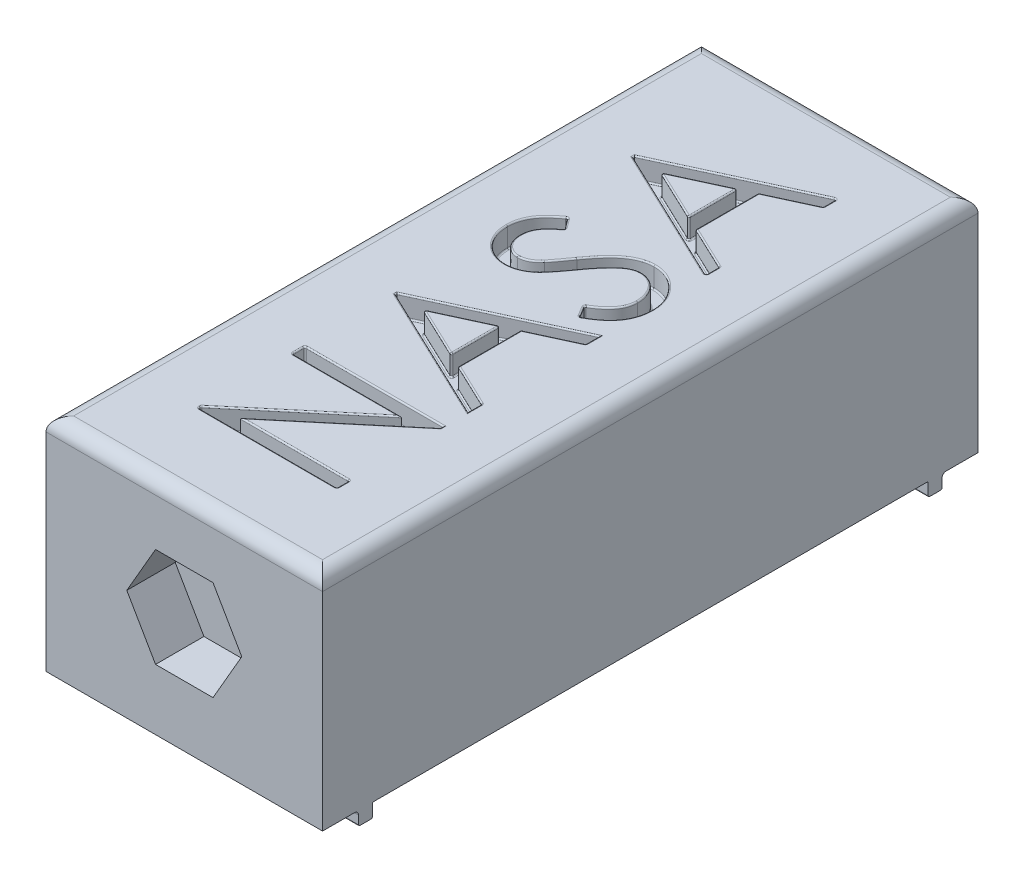
SolidWorks part; units mm, degrees
ref_plane "Front Plane" through (0, 0, 0) normal (0, 0, 1) x (1, 0, 0)
ref_plane "Top Plane" through (0, 0, 0) normal (0, 1, 0) x (1, 0, 0)
ref_plane "Right Plane" through (0, 0, 0) normal (1, 0, 0) x (0, 0, -1)
sketch "Sketch1" plane through (0, 0, 0) normal (0, 1, 0) x (1, 0, 0)
  line L1 (-10, 20) -> (10, 20)
  line L2 (-10, 20) -> (-10, -20)
  line L3 (-10, -20) -> (10, -20)
  line L4 (10, 20) -> (10, -20)
  line L5 (-10, 20) -> (10, -20) construction
  line L6 (-10, -20) -> (10, 20) construction
  point P4 (0, 0)
  dimension "D1" = 40
  dimension "D2" = 20
extrude "Boss-Extrude1" add sketch "Sketch1" along normal blind 16
sketch "Sketch2" plane through (0, 0, 0) normal (0, -1, 0) x (1, 0, 0)
  line L0 (-10, 0) -> (10, 0) construction
  line L1 (-10, 23.7) -> (10, 23.7)
  line L2 (-10, 23.7) -> (-10, 20)
  line L3 (-10, 20) -> (10, 20)
  line L4 (10, 23.7) -> (10, 20)
  line L5 (-10, 23.7) -> (10, 20) construction
  line L6 (-10, 20) -> (10, 23.7) construction
  line L11 (-10, -20) -> (10, -23.7) construction
  line L12 (-10, -23.7) -> (10, -20) construction
  line L13 (-10, -20) -> (-10, 20) construction
  line L14 (10, 20) -> (10, -20) construction
  line L15 (10, -23.7) -> (10, -20)
  line L16 (-10, -20) -> (10, -20)
  line L17 (-10, -23.7) -> (-10, -20)
  line L18 (-10, -23.7) -> (10, -23.7)
  point P4 (0, 21.85)
  point P12 (0, -21.85)
  dimension "D1" = 3.7
extrude "Boss-Extrude2" add sketch "Sketch2" against normal blind 16 contours L2 L1 L4 L3 | L15 L16 L17 L18
sketch "Sketch3" plane through (0, 0, -23.7) normal (0, 0, -1) x (-1, 0, 0)
  line L0 (-10, 16) -> (10, 0) construction
  line L1 (10, 16) -> (-10, 0) construction
  line L2 (10, 0) -> (-10, 0) construction
  line L3 (2.0785, 11.6) -> (-2.0785, 11.6)
  line L4 (-2.0785, 11.6) -> (-4.1569, 8)
  line L5 (-4.1569, 8) -> (-2.0785, 4.4)
  line L6 (-2.0785, 4.4) -> (2.0785, 4.4)
  line L7 (2.0785, 4.4) -> (4.1569, 8)
  line L8 (4.1569, 8) -> (2.0785, 11.6)
  line L9 (10, 16) -> (10, 0) construction
  circle A1 centre (0, 8) radius 3.6 construction
  point P1 (0, 0)
  point P4 (10, 16)
  point P5 (10, 0)
  point P8 (0, 0)
  point P11 (-10, 0)
  point P21 (-10, 16)
  point P23 (0, 0)
  point P24 (10, 0)
  point P25 (-10, 16)
  point P26 (10, 0)
  dimension "D1" = 7.2
extrude "Cut-Extrude8" cut sketch "Sketch3" against normal blind 3.5
fillet "Fillet1" radius 1 4 edges at (0, 16, 23.7) (10, 16, 0) (-10, 16, 0) (0, 16, -23.7)
sketch "Sketch4" plane through (0, 0, 0) normal (0, -1, 0) x (1, 0, 0)
  line L0 (-10, 0) -> (10, 0) construction
  line L1 (-10, -23.7) -> (-10, 23.7) construction
  line L2 (10, 23.7) -> (10, -23.7) construction
  line L3 (-10, -20.1) -> (10, -20.1)
  line L4 (-10, 21.1) -> (10, 21.1)
  line L5 (-10, 21.1) -> (-10, 20.1)
  line L6 (-10, 20.1) -> (10, 20.1)
  line L7 (10, 21.1) -> (10, 20.1)
  line L8 (10, -21.1) -> (10, -20.1)
  line L9 (-10, -21.1) -> (10, -21.1)
  line L10 (-10, -21.1) -> (-10, -20.1)
  line L11 (-10, 23.7) -> (10, 23.7) construction
  line L12 (-10, -23.7) -> (10, -23.7) construction
  dimension "D1" = 1
  dimension "D2" = 20.1
  dimension "D3" = 23.7
  dimension "D4" = 23.7
extrude "Boss-Extrude3" add sketch "Sketch4" along normal blind 1
fillet "Fillet2" radius 0.3 2 edges at (0, 0, 21.1) (0, 0, -21.1)
fillet "Fillet3" radius 0.1 6 edges at (0, 0, 20.1) (0, -1, 20.1) (0, -1, 21.1) (0, 0, -20.1) (0, -1, -21.1) (0, -1, -20.1)
sketch "Sketch5" plane through (0, 16, 0) normal (0, 1, 0) x (1, 0, 0)
  line L0 (-5, 13.8718) -> (5, 18.4872)
  line L1 (-5, 19) -> (5, 19) construction
  line L2 (-5, 19) -> (-5, -19) construction
  line L3 (-5, -19) -> (5, -19) construction
  line L4 (5, 19) -> (5, -19) construction
  line L5 (-5, 19) -> (5, -19) construction
  line L6 (-5, -19) -> (5, 19) construction
  line L7 (5, 18.4872) -> (5, 17.5116)
  line L8 (5, 17.5116) -> (1.7949, 16.0333)
  line L9 (1.7949, 16.0333) -> (1.7949, 11.5)
  line L10 (1.7949, 11.5) -> (5, 9.9796)
  line L11 (5, 9.9796) -> (5, 9)
  line L12 (5, 9) -> (-5, 13.7436)
  line L13 (-5, 13.7436) -> (-5, 13.8718)
  line L14 (-3.0509, 13.7977) -> (0.7692, 11.9868)
  line L15 (0.7692, 11.9868) -> (0.7692, 15.5605)
  line L16 (0.7692, 15.5605) -> (-3.0509, 13.7977)
  line L17 (3.0709, 1.8205) -> (2.5641, 2.6659)
  line L18 (-3.5637, 7.5897) -> (-2.9487, 6.7784)
  line L19 (-5, -3.3077) -> (5, 1.3077)
  line L20 (5, 1.3077) -> (5, 0.3321)
  line L21 (5, 0.3321) -> (1.7949, -1.1462)
  line L22 (1.7949, -1.1462) -> (1.7949, -5.6795)
  line L23 (1.7949, -5.6795) -> (5, -7.1999)
  line L24 (5, -7.1999) -> (5, -8.1795)
  line L25 (5, -8.1795) -> (-5, -3.4359)
  line L26 (-5, -3.4359) -> (-5, -3.3077)
  line L27 (-3.0509, -3.3818) -> (0.7692, -5.1927)
  line L28 (0.7692, -5.1927) -> (0.7692, -1.619)
  line L29 (0.7692, -1.619) -> (-3.0509, -3.3818)
  line L30 (5, -17.6667) -> (-5, -17.6667)
  line L31 (-5, -17.6667) -> (-5, -17.4784)
  line L32 (-5, -17.4784) -> (2.8706, -10.8718)
  line L33 (2.8706, -10.8718) -> (-5, -10.8718)
  line L34 (-5, -10.8718) -> (-5, -9.9744)
  line L35 (-5, -9.9744) -> (5, -9.9744)
  line L36 (5, -9.9744) -> (5, -10.1787)
  line L37 (5, -10.1787) -> (-2.8526, -16.7692)
  line L38 (-2.8526, -16.7692) -> (5, -16.7692)
  line L39 (5, -16.7692) -> (5, -17.6667)
  spline S0 degree 3 poles (2.5641, 2.6659) (2.8182, 2.8123) (3.1746, 3.0434) (3.5782, 3.4069) (3.8151, 3.6782) (4.0012, 3.959) (4.1768, 4.3447) (4.2313, 4.6557) (4.2308, 4.8614) knots 0 0 0 0 0.304646 0.438547 0.562322 0.677433 0.786897 1 1 1 1
  spline S1 degree 3 poles (4.2308, 4.8614) (4.2315, 5.035) (4.2035, 5.2951) (4.1028, 5.6269) (4.0015, 5.8635) (3.8769, 6.0828) (3.73, 6.2781) (3.5603, 6.4431) (3.374, 6.5798) (3.1742, 6.6856) (2.9001, 6.7925) (2.6802, 6.818) (2.5361, 6.8205) knots 0 0 0 0 0.180992 0.270379 0.360478 0.448694 0.532623 0.614316 0.694491 0.772638 0.849284 1 1 1 1
  spline S2 degree 3 poles (2.5361, 6.8205) (2.367, 6.8223) (2.0145, 6.7513) (1.7036, 6.5723) (1.5545, 6.4619) knots 0 0 0 0 0.475391 1 1 1 1
  spline S3 degree 3 poles (1.5545, 6.4619) (1.4328, 6.3699) (1.2488, 6.2136) (1.0132, 5.9727) (0.8183, 5.7594) (0.6149, 5.5213) (0.3198, 5.1576) (0.1064, 4.8629) (-0.0401, 4.6591) knots 0 0 0 0 0.189534 0.299205 0.418374 0.548366 0.688129 1 1 1 1
  spline S4 degree 3 poles (-0.0401, 4.6591) (-0.1817, 4.4567) (-0.3918, 4.1735) (-0.6654, 3.8198) (-0.8433, 3.5991) (-1.005, 3.4095) (-1.1814, 3.2123) (-1.315, 3.0894) (-1.4002, 3.0204) knots 0 0 0 0 0.347082 0.495568 0.628357 0.74552 0.845831 1 1 1 1
  spline S5 degree 3 poles (-1.4002, 3.0204) (-1.5148, 2.9321) (-1.6904, 2.8085) (-1.9406, 2.6776) (-2.13, 2.5996) (-2.3226, 2.5366) (-2.5857, 2.4778) (-2.7878, 2.4609) (-2.9227, 2.4615) knots 0 0 0 0 0.26255 0.388252 0.511531 0.633734 0.755402 1 1 1 1
  spline S6 degree 3 poles (-2.9227, 2.4615) (-3.1319, 2.461) (-3.4432, 2.5005) (-3.8356, 2.6337) (-4.1108, 2.7715) (-4.3623, 2.9493) (-4.5923, 3.1559) (-4.7883, 3.3997) (-4.957, 3.6696) (-5.0902, 3.9635) (-5.2206, 4.3791) (-5.2545, 4.7069) (-5.2564, 4.9255) knots 0 0 0 0 0.165751 0.246237 0.327404 0.408726 0.48963 0.57161 0.655742 0.741224 0.826577 1 1 1 1
  spline S7 degree 3 poles (-5.2564, 4.9255) (-5.2576, 5.1598) (-5.2121, 5.5102) (-5.0601, 5.9547) (-4.9277, 6.2212) (-4.796, 6.4302) (-4.6758, 6.5895) (-4.5377, 6.7517) (-4.3788, 6.9152) (-4.2023, 7.0816) (-3.9337, 7.3132) (-3.7171, 7.4809) (-3.5637, 7.5897) knots 0 0 0 0 0.213204 0.318562 0.426501 0.48334 0.543285 0.607974 0.677199 0.750741 0.828752 1 1 1 1
  spline S8 degree 3 poles (-2.9487, 6.7784) (-3.0714, 6.6855) (-3.2432, 6.5443) (-3.4592, 6.357) (-3.594, 6.2232) (-3.7181, 6.1006) (-3.8225, 5.9795) (-3.9104, 5.8646) (-4.0045, 5.7201) (-4.0947, 5.5371) (-4.2018, 5.2313) (-4.2296, 4.9876) (-4.2308, 4.8253) knots 0 0 0 0 0.18959 0.274128 0.352111 0.423687 0.489026 0.548936 0.601892 0.701259 0.799633 1 1 1 1
  spline S9 degree 3 poles (-4.2308, 4.8253) (-4.2345, 4.6262) (-4.1896, 4.3355) (-4.0351, 3.985) (-3.8739, 3.766) (-3.6815, 3.5854) (-3.3879, 3.4073) (-3.133, 3.3594) (-2.9647, 3.359) knots 0 0 0 0 0.275822 0.401869 0.527875 0.650459 0.765964 1 1 1 1
  spline S10 degree 3 poles (-2.9647, 3.359) (-2.8566, 3.3562) (-2.6965, 3.3791) (-2.4869, 3.4345) (-2.3305, 3.4977) (-2.172, 3.586) (-1.9415, 3.7495) (-1.7811, 3.9055) (-1.6727, 4.018) knots 0 0 0 0 0.216059 0.322956 0.434131 0.553424 0.686081 1 1 1 1
  spline S11 degree 3 poles (-1.6727, 4.018) (-1.6256, 4.0694) (-1.5482, 4.1634) (-1.4371, 4.3126) (-1.3211, 4.4653) (-1.1866, 4.6481) (-0.971, 4.951) (-0.7974, 5.1911) (-0.6771, 5.3622) knots 0 0 0 0 0.124952 0.218094 0.333502 0.468789 0.624938 1 1 1 1
  spline S12 degree 3 poles (-0.6771, 5.3622) (-0.5246, 5.5726) (-0.3011, 5.8765) (0.0093, 6.251) (0.2275, 6.4952) (0.4376, 6.7148) (0.642, 6.9076) (0.8393, 7.0745) (1.0905, 7.2567) (1.4019, 7.4403) (1.9009, 7.6479) (2.2927, 7.718) (2.5501, 7.7179) knots 0 0 0 0 0.187763 0.272381 0.351302 0.424312 0.491882 0.554203 0.610843 0.715918 0.81455 1 1 1 1
  spline S13 degree 3 poles (2.5501, 7.7179) (2.7278, 7.7207) (2.991, 7.6918) (3.3312, 7.6068) (3.5735, 7.5131) (3.8086, 7.3968) (4.0323, 7.2513) (4.2489, 7.0817) (4.4522, 6.8873) (4.6391, 6.6747) (4.8047, 6.4492) (4.9459, 6.2132) (5.0584, 5.964) (5.1469, 5.7044) (5.2338, 5.3384) (5.2572, 5.0533) (5.2564, 4.8614) knots 0 0 0 0 0.121796 0.180952 0.240299 0.299757 0.3608 0.423165 0.488346 0.553642 0.617281 0.680182 0.742142 0.804628 0.868236 1 1 1 1
  spline S14 degree 3 poles (5.2564, 4.8614) (5.2573, 4.7111) (5.2392, 4.4882) (5.19, 4.1962) (5.1325, 3.9858) (5.0625, 3.78) (4.9764, 3.5796) (4.8732, 3.3845) (4.7552, 3.1936) (4.6179, 3.0074) (4.4581, 2.8275) (4.2799, 2.6491) (4.0805, 2.4736) (3.8577, 2.3047) (3.5253, 2.0767) (3.257, 1.9212) (3.0709, 1.8205) knots 0 0 0 0 0.113694 0.169175 0.224155 0.278714 0.333787 0.389234 0.445813 0.503694 0.564283 0.627963 0.694643 0.765377 0.839615 1 1 1 1
  point P4 (0, 0)
  dimension "D1" = 38
  dimension "D2" = 10
extrude "Cut-Extrude7" cut sketch "Sketch5" against normal blind 1.5 contours L0 L7 L8 L9 L10 L11 L12 L13 | L17 S0 S1 S2 S3 S4 S5 S6 S7 L18 S8 S9 S10 S11 S12 S13 S14 | L19 L20 L21 L22 L23 L24 L25 L26 | L30 L31 L32 L33 L34 L35 L36 L37 L38 L39 | L14 L15 L16 | L27 L28 L29
fillet "Fillet5" radius 0.1 124 edges at (-5, 16, -13.8077) (0, 16, -16.1795) (5, 16, -17.9994) (5, 15.25, -18.4872) (3.3974, 16, -16.7724) (5, 15.25, -17.5116) (1.7949, 16, -13.7666) (1.7949, 15.25, -16.0333) (3.3974, 16, -10.7398) (1.7949, 15.25, -11.5) (5, 16, -9.4898) (5, 15.25, -9.9796) (0, 16, -11.3718) (5, 15.25, -9) (0.7692, 14.5, -13.7736) (-1.1408, 14.5, -14.6791) (-1.1408, 14.5, -12.8922) (-5, 14.5, -13.8077) (0, 14.5, -16.1795) (5, 14.5, -17.9994) (3.3974, 14.5, -16.7724) (1.7949, 14.5, -13.7666) (3.3974, 14.5, -10.7398) (5, 14.5, -9.4898) (0, 14.5, -11.3718) (-1.1408, 16, -14.6791) (0.7692, 15.25, -15.5605) (0.7692, 16, -13.7736) (0.7692, 15.25, -11.9868) (-1.1408, 16, -12.8922) (-3.0509, 15.25, -13.7977) (2.8175, 16, -2.2432) (3.0709, 15.25, -1.8205) (2.5641, 15.25, -2.6659) (-3.2562, 16, -7.1841) (-3.5637, 15.25, -7.5897) (-2.9487, 15.25, -6.7784) (2.8175, 14.5, -2.2432) (-3.2562, 14.5, -7.1841) (-5, 16, 3.3718) (0, 16, 1) (5, 16, -0.8199) (3.3974, 16, 0.4071) (5, 15.25, -0.3321) (1.7949, 16, 3.4129) (1.7949, 15.25, 1.1462) (3.3974, 16, 6.4397) (1.7949, 15.25, 5.6795) (5, 16, 7.6897) (5, 15.25, 7.1999) (0, 16, 5.8077) (0.7692, 14.5, 3.4058) (-1.1408, 14.5, 2.5004) (-1.1408, 14.5, 4.2873) (-5, 14.5, 3.3718) (0, 14.5, 1) (5, 14.5, -0.8199) (3.3974, 14.5, 0.4071) (1.7949, 14.5, 3.4129) (3.3974, 14.5, 6.4397) (5, 14.5, 7.6897) (0, 14.5, 5.8077) (-1.1408, 16, 2.5004) (0.7692, 15.25, 1.619) (0.7692, 16, 3.4058) (0.7692, 15.25, 5.1927) (-1.1408, 16, 4.2873) (-3.0509, 15.25, 3.3818) (5, 16, 17.2179) (5, 15.25, 16.7692) (0, 16, 17.6667) (5, 15.25, 17.6667) (-5, 16, 17.5725) (-5, 15.25, 17.6667) (-1.0647, 16, 14.1751) (-5, 15.25, 17.4784) (-1.0647, 16, 10.8718) (-5, 16, 10.4231) (-5, 15.25, 10.8718) (0, 16, 9.9744) (-5, 15.25, 9.9744) (5, 16, 10.0765) (1.0737, 16, 13.474) (1.0737, 16, 16.7692) (5, 14.5, 17.2179) (0, 14.5, 17.6667) (-5, 14.5, 17.5725) (-1.0647, 14.5, 14.1751) (-1.0647, 14.5, 10.8718) (-5, 14.5, 10.4231) (0, 14.5, 9.9744) (5, 14.5, 10.0765) (1.0737, 14.5, 13.474) (1.0737, 14.5, 16.7692)
mirror "Mirror1" about plane through (0, 0, 0) normal (0, 0, 1) of "Cut-Extrude8"
